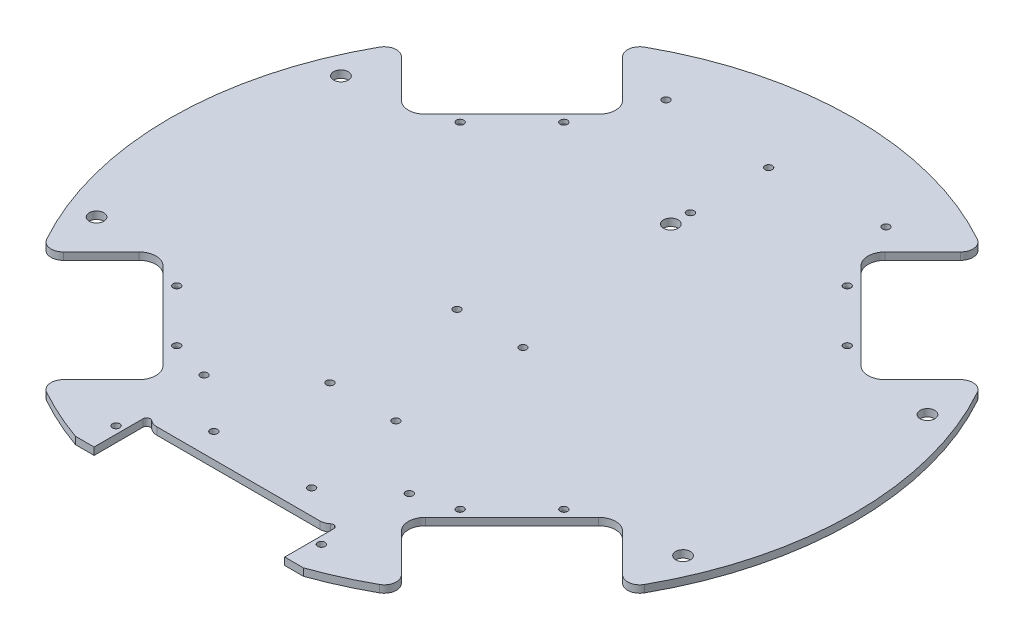
SolidWorks part; units mm, degrees
material "1060 Alloy"
ref_plane "Front Plane" through (0, 0, 0) normal (0, 0, 1) x (1, 0, 0)
ref_plane "Top Plane" through (0, 0, 0) normal (0, 1, 0) x (1, 0, 0)
ref_plane "Right Plane" through (0, 0, 0) normal (1, 0, 0) x (0, 0, -1)
sketch "Sketch1" plane through (0, 0, 0) normal (0, 1, 0) x (1, 0, 0)
  circle A0 centre (0, 0) radius 140
  dimension "D1" = 280
extrude "Boss-Extrude1" add sketch "Sketch1" along normal blind 3
sketch "Sketch7" plane through (0, 3, 0) normal (0, 1, 0) x (1, 0, 0)
  line L0 (-89.1308, -53.7048) -> (-53.7048, -89.1308)
  line L1 (-98.9596, -53.7048) -> (-121.6224, -76.3675)
  line L2 (-53.7048, -98.9596) -> (-76.3675, -121.6224)
  line L3 (-121.6224, -76.3675) -> (-76.3675, -121.6224)
  line L4 (0, 0) -> (-98.9949, -98.9949) construction
  line L7 (0, 0) -> (0, 130) construction
  circle A0 centre (0, 0) radius 140 construction
  arc A1 (-98.9596, -53.7048) -> (-89.1308, -53.7048) centre (-94.0452, -58.6192) cw
  arc A2 (-53.7048, -89.1308) -> (-53.7048, -98.9596) centre (-58.6192, -94.0452) cw
  dimension "D4" = 6.95
  dimension "D1" = 101
  dimension "D2" = 64
  dimension "D3" = 135
extrude "Cut-Extrude4" cut sketch "Sketch7" against normal up to next (3 mm away)
sketch "Sketch9" plane through (0, 3, 0) normal (0, 1, 0) x (1, 0, 0)
  line L1 (-53.7048, -89.1308) -> (-89.1308, -53.7048) construction
  line L4 (-98.9596, -53.7048) -> (-119.0017, -73.7469) construction
  circle A0 centre (-79.196, -57.9828) radius 1.5
  circle A1 centre (-57.9828, -79.196) radius 1.5
  dimension "D4" = 3
  dimension "D1" = 4
  dimension "D2" = 30
  dimension "D3" = 17
  dimension "D5" = 4
extrude "Cut-Extrude6" cut sketch "Sketch9" against normal up to next (3 mm away)
fillet "Fillet1" radius 5 2 edges at (-73.7469, 1.5, 119.0017) (-119.0017, 1.5, 73.7469)
pattern_circular "CirPattern1" count 4 over 360 about axis through (0, 0, 0) along (0, 1, 0) of "Cut-Extrude4", "Fillet1", "Cut-Extrude6"
sketch "Sketch2" plane through (0, 3, 0) normal (0, 1, 0) x (1, 0, 0)
  line L0 (-46.6476, -132) -> (-39, -132)
  line L1 (-39, -132) -> (-39, -112)
  line L2 (-33.3467, -112) -> (33.3467, -112)
  line L3 (39, -112) -> (39, -132)
  line L4 (39, -132) -> (46.6476, -132)
  line L5 (46.6476, -132) -> (46.6476, -140)
  line L6 (46.6476, -140) -> (-46.6476, -140)
  line L7 (-46.6476, -140) -> (-46.6476, -132)
  circle A0 centre (0, 0) radius 140 construction
  arc A1 (-39, -112) -> (-36.5415, -110.8462) centre (-37.5, -112) cw
  arc A2 (-33.3467, -112) -> (-36.5415, -110.8462) centre (-33.3467, -107) cw
  arc A3 (39, -112) -> (36.5415, -110.8462) centre (37.5, -112) ccw
  arc A4 (33.3467, -112) -> (36.5415, -110.8462) centre (33.3467, -107) ccw
  dimension "D5" = 1.5
  dimension "D6" = 5
  dimension "D1" = 8
  dimension "D2" = 20
  dimension "D3" = 78
  dimension "D4" = 7.6476
extrude "Cut-Extrude1" cut sketch "Sketch2" against normal up to next
fillet "Fillet3" radius 1.5 8 edges at (57.9828, 0, 80.696) (79.196, 0, 59.4828) (79.196, 0, -56.4828) (57.9828, 0, -77.696) (-57.9828, 0, -77.696) (-79.196, 0, -56.4828) (-57.9828, 0, 80.696) (-79.196, 0, 59.4828)
sketch "Sketch10" plane through (0, 3, 0) normal (0, 1, 0) x (1, 0, 0)
  circle A0 centre (-13.5, -61) radius 1.5
  circle A1 centre (13.5, -61) radius 1.5
  circle A2 centre (-13.5, -9) radius 1.5
  circle A3 centre (13.5, -9) radius 1.5
  dimension "D3" = 3
  dimension "D1" = 13.5
  dimension "D2" = 27
  dimension "D4" = 61
  dimension "D5" = 52
extrude "Cut-Extrude7" cut sketch "Sketch10" against normal up to next
sketch "Sketch11" plane through (0, 3, 0) normal (0, 1, 0) x (1, 0, 0)
  line L0 (33.3467, -112) -> (-33.3467, -112) construction
  circle A0 centre (-20, -102) radius 1.5
  circle A1 centre (20, -102) radius 1.5
  dimension "D1" = 3
  dimension "D2" = 40
  dimension "D3" = 10
  dimension "D4" = 20
extrude "Cut-Extrude8" cut sketch "Sketch11" against normal up to next
sketch "Sketch13" plane through (0, 3, 0) normal (0, 1, 0) x (1, 0, 0)
  line L1 (-39, -132) -> (-46.6476, -132) construction
  line L2 (-39, -112) -> (-39, -132) construction
  line L3 (39, -132) -> (39, -112) construction
  circle A0 centre (-42, -84) radius 1.5
  circle A1 centre (-42, -120) radius 1.5
  circle A2 centre (42, -120) radius 1.5
  circle A3 centre (42, -84) radius 1.5
  dimension "D1" = 3
  dimension "D2" = 12
  dimension "D3" = 36
  dimension "D4" = 3
  dimension "D5" = 3
extrude "Cut-Extrude9" cut sketch "Sketch13" against normal up to next
sketch "Sketch16" plane through (0, 3, 0) normal (0, 1, 0) x (1, 0, 0)
  circle A0 centre (0, 73) radius 1.5
  circle A1 centre (-45, 108) radius 1.5
  circle A2 centre (45, 108) radius 1.5
  circle A3 centre (0, 105) radius 1.5
  circle A4 centre (0, 65) radius 3
  dimension "D2" = 3
  dimension "D5" = 6
  dimension "D1" = 73
  dimension "D3" = 108
  dimension "D4" = 90
  dimension "D6" = 32
  dimension "D7" = 65
extrude "Cut-Extrude12" cut sketch "Sketch16" against normal up to next
sketch "Sketch17" plane through (0, 3, 0) normal (0, 1, 0) x (1, 0, 0)
  circle A0 centre (-120, 50) radius 3
  circle A1 centre (-120, -50) radius 3
  circle A2 centre (120, 50) radius 3
  circle A3 centre (120, -50) radius 3
  dimension "D1" = 6
  dimension "D2" = 50
  dimension "D3" = 50
  dimension "D4" = 120
  dimension "D5" = 120
extrude "Cut-Extrude13" cut sketch "Sketch17" against normal up to next
